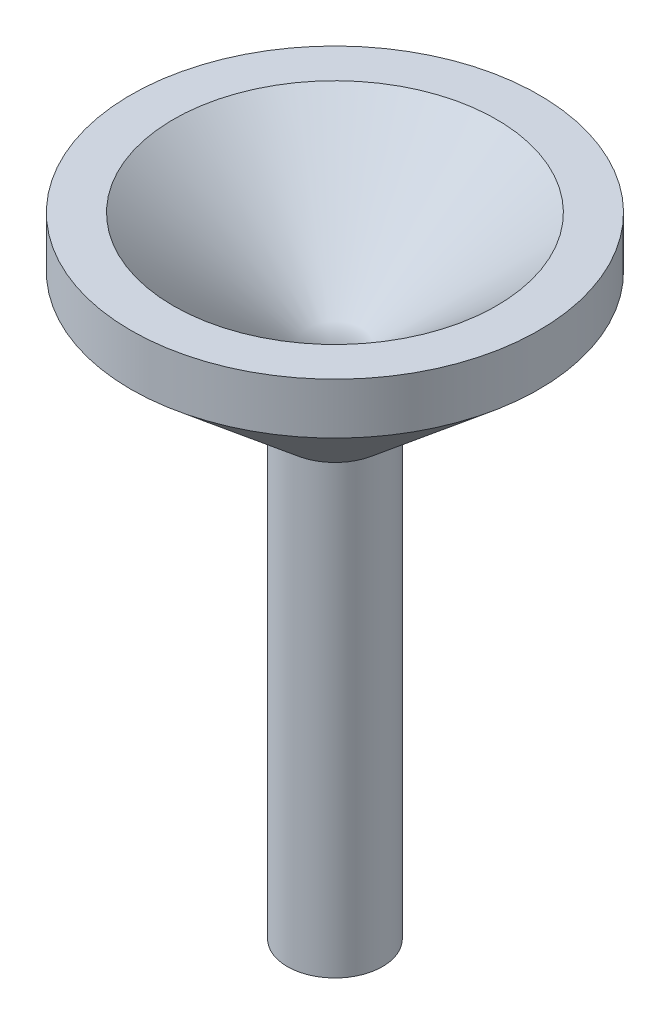
SolidWorks part; units mm, degrees
ref_plane "Front Plane" through (0, 0, 0) normal (0, 0, 1) x (1, 0, 0)
ref_plane "Top Plane" through (0, 0, 0) normal (0, 1, 0) x (1, 0, 0)
ref_plane "Right Plane" through (0, 0, 0) normal (1, 0, 0) x (0, 0, -1)
sketch "Sketch1" plane through (0, 0, 0) normal (0, 0, 1) x (1, 0, 0)
  line L0 (0, 178.392) -> (0, -336.5401) construction
  line L1 (0, 0) -> (95, 80)
  line L2 (95, 80) -> (120, 80)
  line L3 (120, 80) -> (120, 50)
  line L4 (120, 50) -> (28, -27.4737)
  line L5 (28, -27.4737) -> (28, -290)
  line L6 (28, -290) -> (0, -290)
  line L7 (0, 0) -> (0, -290)
  point P5 (0, 0)
  point P11 (0, -336.5401)
  dimension "D1" = 190
  dimension "D2" = 80
  dimension "D3" = 30
  dimension "D4" = 240
  dimension "D5" = 370
  dimension "D6" = 56
revolve "Revolve1" add sketch "Sketch1" angle 360 about L0
